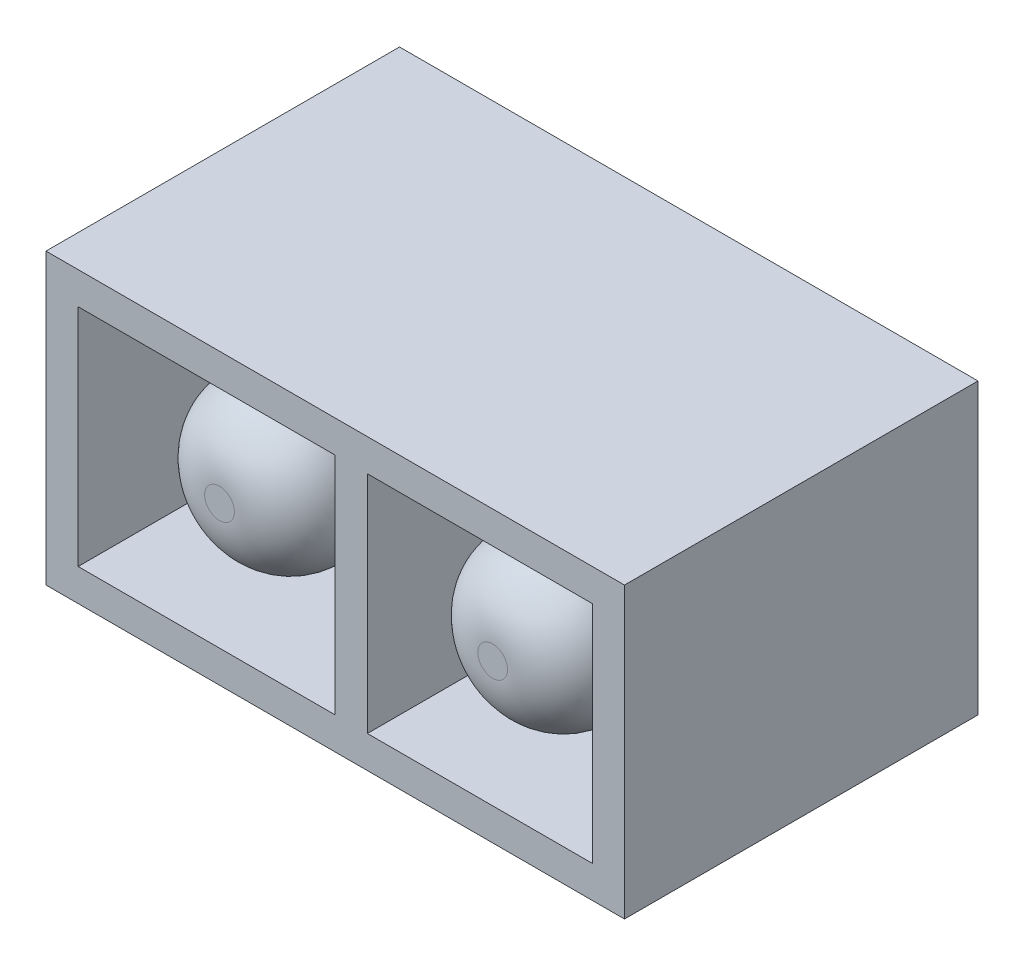
SolidWorks part; units mm, degrees
ref_plane "Front Plane" through (0, 0, 0) normal (0, 0, 1) x (1, 0, 0)
ref_plane "Top Plane" through (0, 0, 0) normal (0, 1, 0) x (1, 0, 0)
ref_plane "Right Plane" through (0, 0, 0) normal (1, 0, 0) x (0, 0, -1)
sketch "Sketch1" plane through (0, 0, 0) normal (0, 0, 1) x (1, 0, 0)
  line L0 (0, 2.25) -> (0, -2.25)
  line L1 (4.5, 2.25) -> (-4.5, 2.25)
  line L2 (4.5, 2.25) -> (4.5, -2.25)
  line L3 (4.5, -2.25) -> (-4.5, -2.25)
  line L4 (-4.5, 2.25) -> (-4.5, -2.25)
  line L5 (0, -2.25) -> (0, 2.25) construction
  line L6 (4.5, 0) -> (-4.5, 0) construction
  line L11 (0, -2.25) -> (0, 2.25) construction
  line L12 (0.25, 0) -> (-0.25, 0) construction
  point P0 (0, 0)
  point P4 (0, 0)
  dimension "D1" = 9
  dimension "D2" = 4.5
extrude "Extrude-Thin2" add sketch "Sketch1" along normal blind 5 thin thin type one direction reverse wall 0.5
sketch "Sketch2" plane through (0, 0, 0) normal (0, 0, -1) x (-1, 0, 0)
  line L0 (-4.5, -2.25) -> (-4.5, 2.25)
  line L1 (-4.5, -2.25) -> (4.5, -2.25)
  line L2 (-4.5, 2.25) -> (4.5, 2.25)
  line L3 (4.5, -2.25) -> (4.5, 2.25)
  line L4 (4.5, 2.25) -> (4.5, -2.25) construction
extrude "Boss-Extrude1" add sketch "Sketch2" along normal blind 0.5
sketch "Sketch4" plane through (0, 0, 0) normal (0, 0, 1) x (1, 0, 0)
  circle A0 centre (2.25, 0) radius 1.5
  circle A1 centre (-2, 0) radius 1.5
  dimension "D1" = 3
extrude "Boss-Extrude3" add sketch "Sketch4" along normal blind 4.8 draft 4
fillet "Fillet1" radius 1 2 edges at (-0.8356, 0, 4.8) (3.4144, 0, 4.8)
